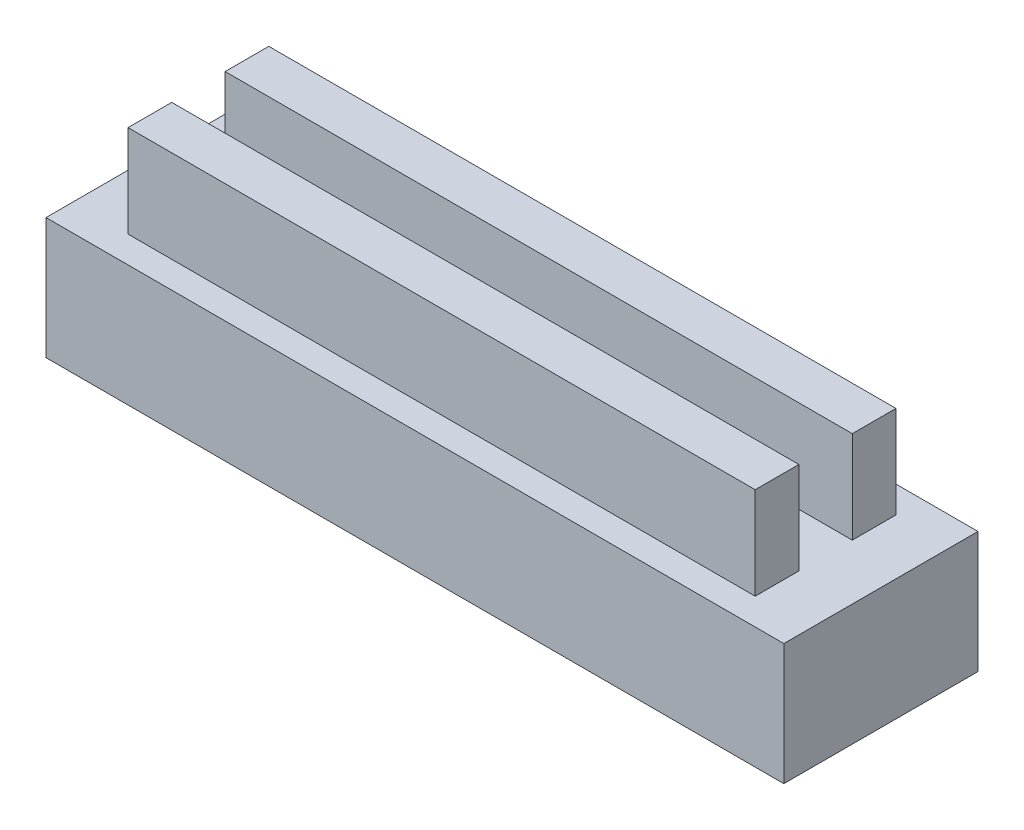
SolidWorks part; units mm, degrees
ref_plane "Front Plane" through (0, 0, 0) normal (0, 0, 1) x (1, 0, 0)
ref_plane "Top Plane" through (0, 0, 0) normal (0, 1, 0) x (1, 0, 0)
ref_plane "Right Plane" through (0, 0, 0) normal (1, 0, 0) x (0, 0, -1)
sketch "Sketch1" plane through (0, 0, 0) normal (0, 1, 0) x (1, 0, 0)
  line L1 (7.6, -2) -> (-7.6, -2)
  line L2 (7.6, -2) -> (7.6, 2)
  line L3 (7.6, 2) -> (-7.6, 2)
  line L4 (-7.6, -2) -> (-7.6, 2)
  line L5 (7.6, -2) -> (-7.6, 2) construction
  line L6 (7.6, 2) -> (-7.6, -2) construction
  point P0 (0, 0)
  dimension "D1" = 4
  dimension "D2" = 15.2
extrude "Boss-Extrude1" add sketch "Sketch1" along normal blind 2.5
sketch "Sketch2" plane through (0, 2.5, 0) normal (0, 1, 0) x (1, 0, 0)
  line L0 (-7.6, 0) -> (7.6, 0) construction
  line L1 (-7.6, 2) -> (-7.6, -2) construction
  line L2 (7.6, -2) -> (7.6, 2) construction
  line L3 (-7.6, 1) -> (7.6, 1) construction
  line L4 (7.6, 2) -> (-7.6, 2) construction
  line L5 (-7.6, -1) -> (7.6, -1) construction
  line L6 (-7.6, -2) -> (7.6, -2) construction
  line L8 (6.46, -1.45) -> (-6.46, -1.45)
  line L9 (6.46, -1.45) -> (6.46, -0.55)
  line L10 (6.46, -0.55) -> (-6.46, -0.55)
  line L11 (-6.46, -1.45) -> (-6.46, -0.55)
  line L12 (6.46, -1.45) -> (-6.46, -0.55) construction
  line L13 (6.46, -0.55) -> (-6.46, -1.45) construction
  line L14 (6.46, 0.55) -> (-6.46, 0.55)
  line L15 (6.46, 0.55) -> (6.46, 1.45)
  line L16 (6.46, 1.45) -> (-6.46, 1.45)
  line L17 (-6.46, 0.55) -> (-6.46, 1.45)
  line L18 (6.46, 0.55) -> (-6.46, 1.45) construction
  line L19 (6.46, 1.45) -> (-6.46, 0.55) construction
  point P14 (0, -1)
  point P19 (0, 1)
  dimension "D1" = 1
  dimension "D2" = 1
  dimension "D3" = 12.92
  dimension "D4" = 0.9
extrude "Boss-Extrude2" add sketch "Sketch2" along normal blind 1.9
